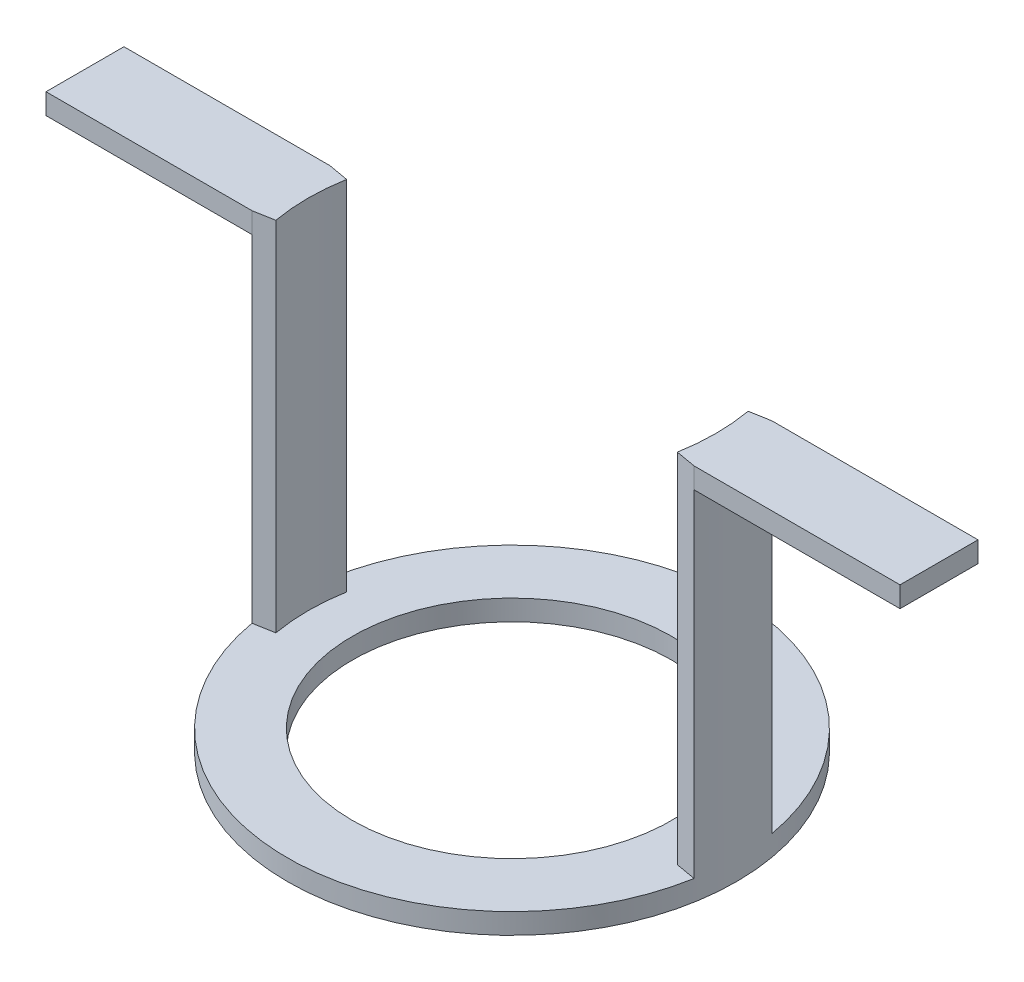
SolidWorks part; units mm, degrees
ref_plane "Front Plane" through (0, 0, 0) normal (0, 0, 1) x (1, 0, 0)
ref_plane "Top Plane" through (0, 0, 0) normal (0, 1, 0) x (1, 0, 0)
ref_plane "Right Plane" through (0, 0, 0) normal (1, 0, 0) x (0, 0, -1)
sketch "Sketch1" plane through (0, 0, 0) normal (0, 1, 0) x (1, 0, 0)
  circle A0 centre (0, 0) radius 21.8
extrude "Boss-Extrude1" add sketch "Sketch1" along normal blind 2
sketch "Sketch2" plane through (0, 2, 0) normal (0, 1, 0) x (1, 0, 0)
  circle A0 centre (0, 0) radius 15.5
extrude "Cut-Extrude1" cut sketch "Sketch2" against normal blind 16
sketch "Sketch3" plane through (0, 2, 0) normal (0, 1, 0) x (1, 0, 0)
  line L0 (-19.4992, 3.4382) -> (-21.4688, 3.7855)
  line L1 (-19.4992, -3.4382) -> (-21.4688, -3.7855)
  line L2 (21.4688, -3.7855) -> (19.499, -3.4382)
  line L3 (21.4688, 3.7855) -> (19.499, 3.4382)
  arc A0 (-19.8, 0) -> (-19.4992, -3.4382) centre (0, 0) ccw
  arc A1 (-19.8, 0) -> (-19.4992, 3.4382) centre (0, 0) cw
  arc A2 (-21.8, 0) -> (-21.4688, -3.7855) centre (0, 0) ccw
  circle A3 centre (0, 0) radius 21.8 construction
  arc A4 (19.7998, 0) -> (19.499, 3.4382) centre (0, 0) ccw
  arc A5 (19.7998, 0) -> (19.499, -3.4382) centre (0, 0) cw
  arc A6 (21.8, 0) -> (21.4688, 3.7855) centre (0, 0) ccw
  arc A7 (21.8, 0) -> (21.4688, -3.7855) centre (0, 0) cw
  arc A8 (-21.8, 0) -> (-21.4688, 3.7855) centre (0, 0) cw
extrude "Boss-Extrude2" add sketch "Sketch3" along normal blind 34.7
sketch "Sketch4" plane through (0, 0, 0) normal (1, 0, 0) x (0, 0, -1)
  line L0 (-3.7855, 36.7) -> (-3.7855, 2) construction
  line L1 (3.7855, 36.7) -> (-3.7855, 36.7)
  line L2 (3.7855, 36.7) -> (3.7855, 34.6889)
  line L3 (3.7855, 34.6889) -> (-3.7855, 34.6889)
  line L4 (-3.7855, 36.7) -> (-3.7855, 34.6889)
extrude "Boss-Extrude3" add sketch "Sketch4" against normal up to surface (13.5312 mm away) from offset 35
sketch "Sketch5" plane through (35, 0, 0) normal (1, 0, 0) x (0, 0, -1)
  line L1 (3.7855, 34.6889) -> (-3.7855, 34.6889)
  line L2 (3.7855, 34.6889) -> (3.7855, 36.7)
  line L3 (3.7855, 36.7) -> (-3.7855, 36.7)
  line L4 (-3.7855, 34.6889) -> (-3.7855, 36.7)
extrude "Boss-Extrude4" add sketch "Sketch5" along normal blind 3
sketch "Sketch6" plane through (38, 0, 0) normal (1, 0, 0) x (0, 0, -1)
  line L0 (-3.7855, 36.7) -> (-3.7855, 34.6889) construction
  line L1 (3.7855, 34.6889) -> (-3.7855, 34.6889)
  line L2 (3.7855, 34.6889) -> (3.7855, 36.7)
  line L3 (3.7855, 36.7) -> (-3.7855, 36.7)
  line L4 (-3.7855, 34.6889) -> (-3.7855, 36.7)
  line L5 (3.7855, 36.7) -> (-3.7855, 36.7) construction
extrude "Boss-Extrude5" add sketch "Sketch6" along normal blind 3.47
sketch "Sketch7" plane through (0, 0, 0) normal (1, 0, 0) x (0, 0, -1)
  line L0 (3.7855, 36.7) -> (-3.7855, 36.7) construction
  line L1 (3.7855, 36.7) -> (-3.7855, 36.7)
  line L2 (3.7855, 36.7) -> (3.7855, 34.6889)
  line L3 (3.7855, 34.6889) -> (-3.7855, 34.6889)
  line L4 (-3.7855, 36.7) -> (-3.7855, 34.6889)
  line L5 (3.7855, 36.7) -> (3.7855, 2) construction
extrude "Boss-Extrude6" add sketch "Sketch7" along normal up to surface (13.5312 mm away) from offset 35
ref_plane "Plane1" through (-35, 34.6889, 3.7855) normal (-1, 0, 0) x (0, 0, 1)
sketch "Sketch8" plane through (-35, 34.6889, 3.7855) normal (-1, 0, 0) x (0, 0, 1)
  line L1 (-7.5711, 2.0111) -> (0, 2.0111)
  line L2 (-7.5711, 2.0111) -> (-7.5711, 0)
  line L3 (-7.5711, 0) -> (0, 0)
  line L4 (0, 2.0111) -> (0, 0)
extrude "Boss-Extrude7" add sketch "Sketch8" along normal blind 6.47
